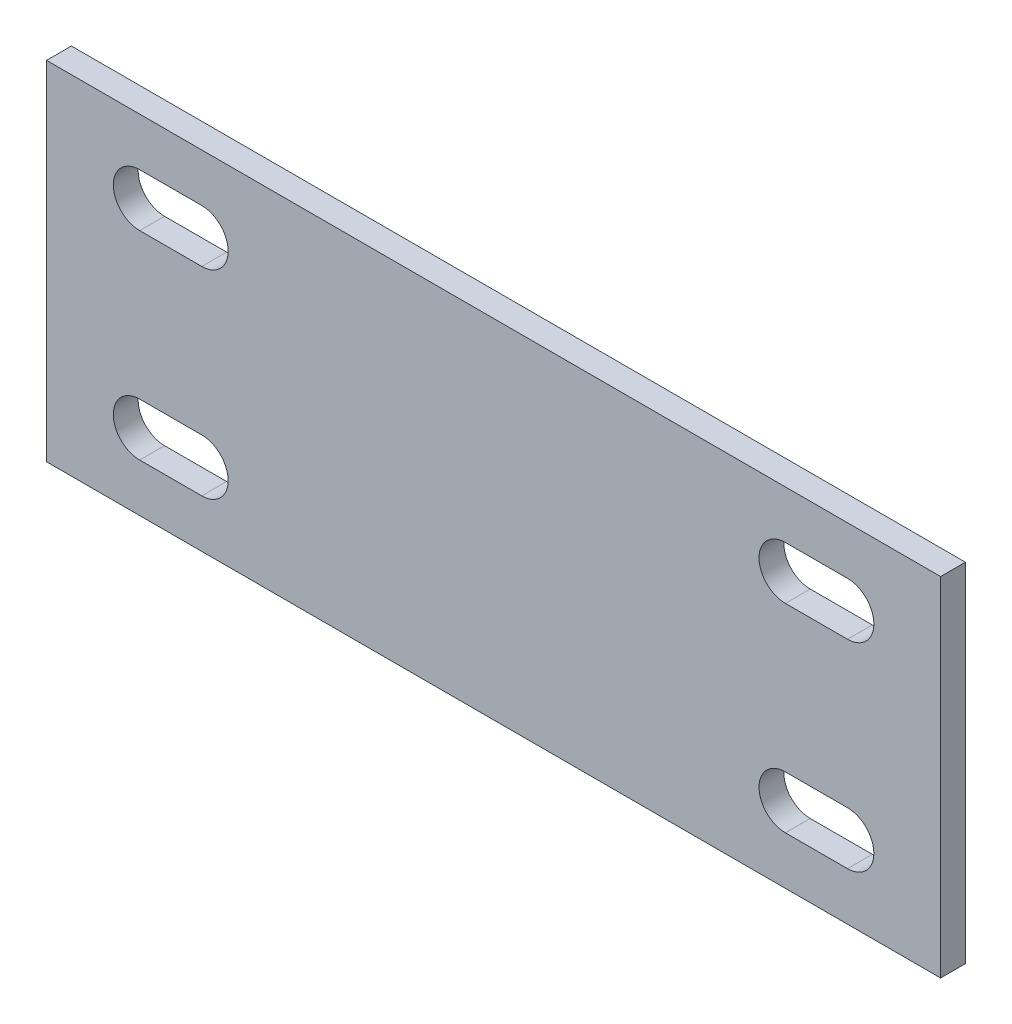
SolidWorks part; units mm, degrees
material "304, 316 OR 302 SSTL"
ref_plane "Front" through (0, 0, 0) normal (0, 0, 1) x (1, 0, 0)
ref_plane "Top" through (0, 0, 0) normal (0, 1, 0) x (1, 0, 0)
ref_plane "Right" through (0, 0, 0) normal (1, 0, 0) x (0, 0, -1)
sketch "Sketch1" plane through (0, 0, 0) normal (0, 0, 1) x (1, 0, 0)
  line L1 (0, 0) -> (228.6, 0)
  line L2 (0, 0) -> (0, 88.9)
  line L3 (0, 88.9) -> (228.6, 88.9)
  line L4 (228.6, 0) -> (228.6, 88.9)
  dimension "D1" = 228.6
  dimension "D2" = 88.9
extrude "Boss-Extrude1" add sketch "Sketch1" along normal blind 6.35
sketch "Sketch2" plane through (0, 0, 6.35) normal (0, 0, 1) x (1, 0, 0)
  line L0 (23.8125, 69.85) -> (39.6875, 69.85) construction
  line L1 (23.8125, 76.5937) -> (39.6875, 76.5937)
  line L2 (23.8125, 63.1063) -> (39.6875, 63.1063)
  line L3 (23.8125, 19.05) -> (39.6875, 19.05) construction
  line L4 (23.8125, 25.7937) -> (39.6875, 25.7937)
  line L5 (23.8125, 12.3063) -> (39.6875, 12.3063)
  line L6 (31.75, 69.85) -> (31.75, 19.05) construction
  line L7 (228.6, 44.45) -> (31.75, 44.45) construction
  line L8 (228.6, 0) -> (228.6, 88.9) construction
  line L9 (0, 88.9) -> (0, 0) construction
  arc A0 (23.8125, 76.5937) -> (23.8125, 63.1063) centre (23.8125, 69.85) ccw
  arc A1 (39.6875, 63.1063) -> (39.6875, 76.5937) centre (39.6875, 69.85) ccw
  arc A2 (23.8125, 25.7937) -> (23.8125, 12.3063) centre (23.8125, 19.05) ccw
  arc A3 (39.6875, 12.3063) -> (39.6875, 25.7937) centre (39.6875, 19.05) ccw
  point P2 (31.75, 69.85)
  point P7 (31.75, 19.05)
  dimension "D3" = 13.4874
  dimension "D1" = 50.8
  dimension "D2" = 15.875
  dimension "D4" = 31.75
extrude "Cut-Extrude1" cut sketch "Sketch2" against normal through all
pattern_linear "LPattern1" count 2 spacing 165.1 along (1, 0, 0) of "Cut-Extrude1"
